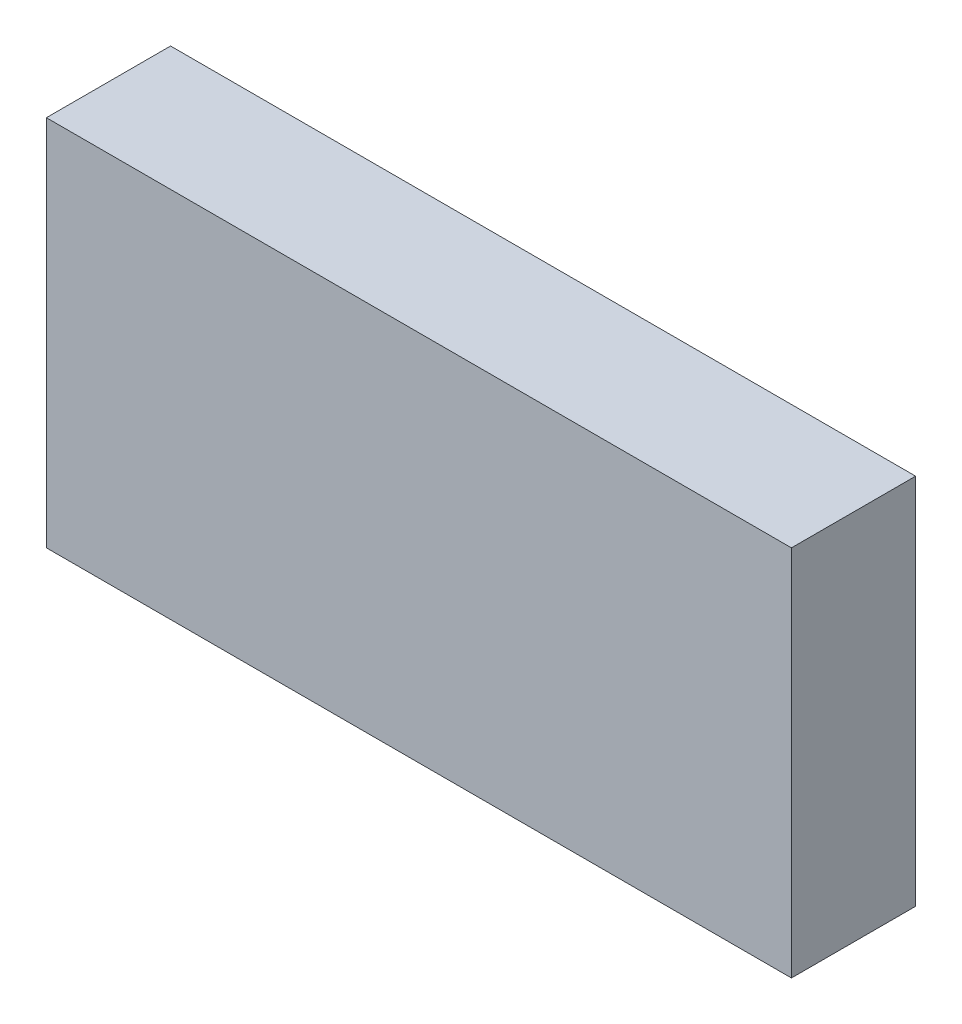
SolidWorks part; units mm, degrees
ref_plane "Front Plane" through (0, 0, 0) normal (0, 0, 1) x (1, 0, 0)
ref_plane "Top Plane" through (0, 0, 0) normal (0, 1, 0) x (1, 0, 0)
ref_plane "Right Plane" through (0, 0, 0) normal (1, 0, 0) x (0, 0, -1)
sketch "Sketch1" plane through (0, 0, 0) normal (0, 0, 1) x (1, 0, 0)
  line L1 (0, 0) -> (30, 0)
  line L2 (0, 0) -> (0, 15)
  line L3 (0, 15) -> (30, 15)
  line L4 (30, 0) -> (30, 15)
  dimension "D1" = 30
  dimension "D2" = 15
extrude "Boss-Extrude1" add sketch "Sketch1" along normal blind 5
